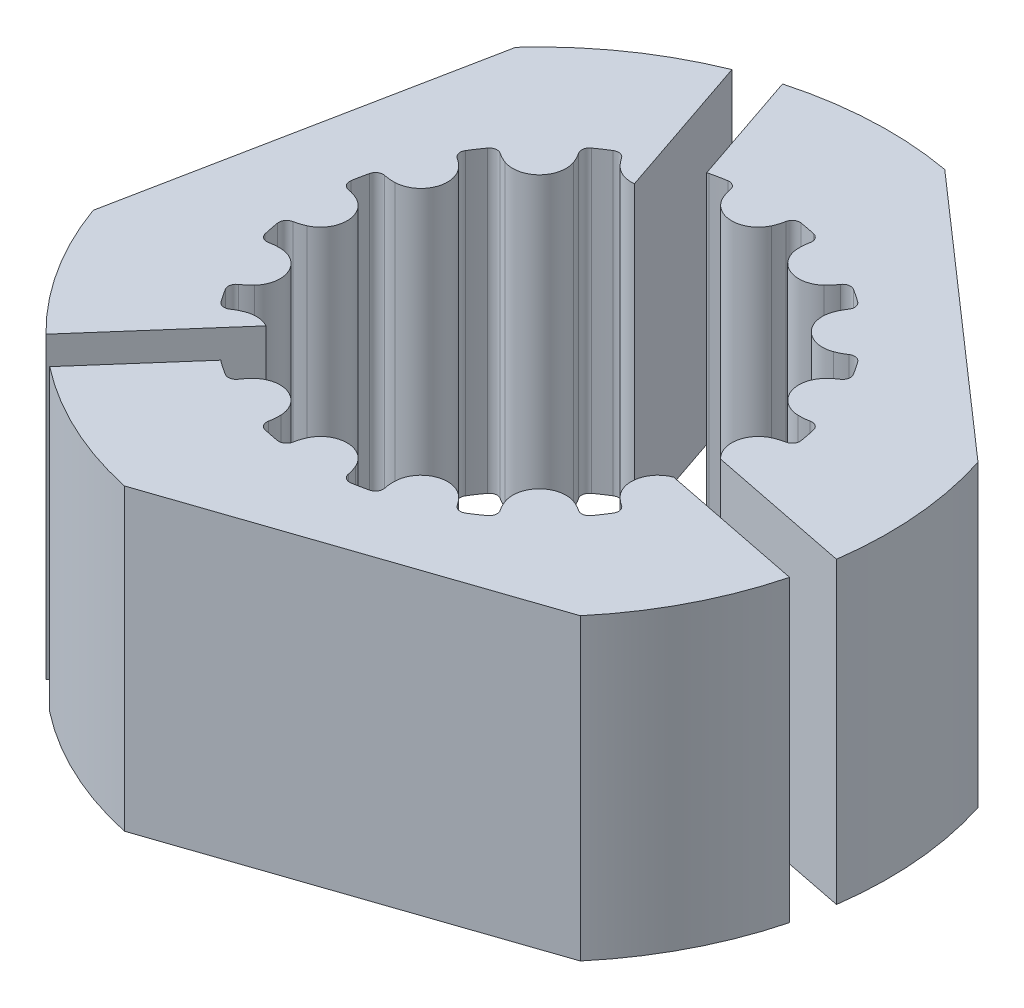
SolidWorks part; units mm, degrees
material "Alum Plate"
ref_plane "Front Plane" through (0, 0, 0) normal (0, 0, 1) x (1, 0, 0)
ref_plane "Top Plane" through (0, 0, 0) normal (0, 1, 0) x (1, 0, 0)
ref_plane "Right Plane" through (0, 0, 0) normal (1, 0, 0) x (0, 0, -1)
other "Bounding Box"
ref_plane "Default Plane" through (-8.9266, -12.7485, 0) normal (-0.1736, 0.9848, 0) x (0.9848, 0.1736, 0)
sketch "Sketch1" plane through (0, 0, 0) normal (0, 1, 0) x (1, 0, 0)
  line L0 (0, -7.8245) -> (0, 0) construction
  circle A0 centre (0, 0) radius 2.5
  arc B0 (-1.8508, -6.777) -> (-1.6633, -7.0715) centre (-1.6061, -6.8282) ccw
  arc B1 (-1.6633, -7.0715) -> (-1.1695, -7.1697) centre (0, 0) ccw
  arc B2 (-1.1695, -7.1697) -> (-0.8836, -6.9694) centre (-1.1292, -6.923) ccw
  arc B3 (-0.7739, -6.6229) -> (-0.8836, -6.9694) centre (0.61, -7.2516) ccw
  arc B4 (0.7739, -6.6229) -> (-0.7739, -6.6229) centre (0, -6.9745) ccw
  arc B5 (0.8836, -6.9694) -> (0.7739, -6.6229) centre (-0.61, -7.2516) ccw
  arc B6 (0.8836, -6.9694) -> (1.1695, -7.1697) centre (1.1292, -6.923) ccw
  arc B7 (1.1695, -7.1697) -> (1.6633, -7.0715) centre (0, 0) ccw
  arc B8 (1.6633, -7.0715) -> (1.8508, -6.777) centre (1.6061, -6.8282) ccw
  arc B9 (1.8195, -6.4149) -> (1.8508, -6.777) centre (3.3386, -6.4662) ccw
  arc B10 (3.2495, -5.8226) -> (1.8195, -6.4149) centre (2.669, -6.4436) ccw
  arc B11 (3.4834, -6.1008) -> (3.2495, -5.8226) centre (2.2115, -6.9331) ccw
  arc B12 (3.4834, -6.1008) -> (3.8242, -6.1764) centre (3.6926, -5.9639) ccw
  arc B13 (3.8242, -6.1764) -> (4.2428, -5.8967) centre (0, 0) ccw
  arc B14 (4.2428, -5.8967) -> (4.3033, -5.5529) centre (4.0968, -5.6938) ccw
  arc B15 (4.1359, -5.2303) -> (4.3033, -5.5529) centre (5.559, -4.6963) ccw
  arc B16 (5.2303, -4.1359) -> (4.1359, -5.2303) centre (4.9317, -4.9317) ccw
  arc B17 (5.5529, -4.3033) -> (5.2303, -4.1359) centre (4.6963, -5.559) ccw
  arc B18 (5.5529, -4.3033) -> (5.8967, -4.2428) centre (5.6938, -4.0968) ccw
  arc B19 (5.8967, -4.2428) -> (6.1764, -3.8242) centre (0, 0) ccw
  arc B20 (6.1764, -3.8242) -> (6.1008, -3.4834) centre (5.9639, -3.6926) ccw
  arc B21 (5.8226, -3.2495) -> (6.1008, -3.4834) centre (6.9331, -2.2115) ccw
  arc B22 (6.4149, -1.8195) -> (5.8226, -3.2495) centre (6.4436, -2.669) ccw
  arc B23 (6.777, -1.8508) -> (6.4149, -1.8195) centre (6.4662, -3.3386) ccw
  arc B24 (6.777, -1.8508) -> (7.0715, -1.6633) centre (6.8282, -1.6061) ccw
  arc B25 (7.0715, -1.6633) -> (7.1697, -1.1695) centre (0, 0) ccw
  arc B26 (7.1697, -1.1695) -> (6.9694, -0.8836) centre (6.923, -1.1292) ccw
  arc B27 (6.6229, -0.7739) -> (6.9694, -0.8836) centre (7.2516, 0.61) ccw
  arc B28 (6.6229, 0.7739) -> (6.6229, -0.7739) centre (6.9745, 0) ccw
  arc B29 (6.9694, 0.8836) -> (6.6229, 0.7739) centre (7.2516, -0.61) ccw
  arc B30 (6.9694, 0.8836) -> (7.1697, 1.1695) centre (6.923, 1.1292) ccw
  arc B31 (7.1697, 1.1695) -> (7.0715, 1.6633) centre (0, 0) ccw
  arc B32 (7.0715, 1.6633) -> (6.777, 1.8508) centre (6.8282, 1.6061) ccw
  arc B33 (6.4149, 1.8195) -> (6.777, 1.8508) centre (6.4662, 3.3386) ccw
  arc B34 (5.8226, 3.2495) -> (6.4149, 1.8195) centre (6.4436, 2.669) ccw
  arc B35 (6.1008, 3.4834) -> (5.8226, 3.2495) centre (6.9331, 2.2115) ccw
  arc B36 (6.1008, 3.4834) -> (6.1764, 3.8242) centre (5.9639, 3.6926) ccw
  arc B37 (6.1764, 3.8242) -> (5.8967, 4.2428) centre (0, 0) ccw
  arc B38 (5.8967, 4.2428) -> (5.5529, 4.3033) centre (5.6938, 4.0968) ccw
  arc B39 (5.2303, 4.1359) -> (5.5529, 4.3033) centre (4.6963, 5.559) ccw
  arc B40 (4.1359, 5.2303) -> (5.2303, 4.1359) centre (4.9317, 4.9317) ccw
  arc B41 (4.3033, 5.5529) -> (4.1359, 5.2303) centre (5.559, 4.6963) ccw
  arc B42 (4.3033, 5.5529) -> (4.2428, 5.8967) centre (4.0968, 5.6938) ccw
  arc B43 (4.2428, 5.8967) -> (3.8242, 6.1764) centre (0, 0) ccw
  arc B44 (3.8242, 6.1764) -> (3.4834, 6.1008) centre (3.6926, 5.9639) ccw
  arc B45 (3.2495, 5.8226) -> (3.4834, 6.1008) centre (2.2115, 6.9331) ccw
  arc B46 (1.8195, 6.4149) -> (3.2495, 5.8226) centre (2.669, 6.4436) ccw
  arc B47 (1.8508, 6.777) -> (1.8195, 6.4149) centre (3.3386, 6.4662) ccw
  arc B48 (1.8508, 6.777) -> (1.6633, 7.0715) centre (1.6061, 6.8282) ccw
  arc B49 (1.6633, 7.0715) -> (1.1695, 7.1697) centre (0, 0) ccw
  arc B50 (1.1695, 7.1697) -> (0.8836, 6.9694) centre (1.1292, 6.923) ccw
  arc B51 (0.7739, 6.6229) -> (0.8836, 6.9694) centre (-0.61, 7.2516) ccw
  arc B52 (-0.7739, 6.6229) -> (0.7739, 6.6229) centre (0, 6.9745) ccw
  arc B53 (-0.8836, 6.9694) -> (-0.7739, 6.6229) centre (0.61, 7.2516) ccw
  arc B54 (-0.8836, 6.9694) -> (-1.1695, 7.1697) centre (-1.1292, 6.923) ccw
  arc B55 (-1.1695, 7.1697) -> (-1.6633, 7.0715) centre (0, 0) ccw
  arc B56 (-1.6633, 7.0715) -> (-1.8508, 6.777) centre (-1.6061, 6.8282) ccw
  arc B57 (-1.8195, 6.4149) -> (-1.8508, 6.777) centre (-3.3386, 6.4662) ccw
  arc B58 (-3.2495, 5.8226) -> (-1.8195, 6.4149) centre (-2.669, 6.4436) ccw
  arc B59 (-3.4834, 6.1008) -> (-3.2495, 5.8226) centre (-2.2115, 6.9331) ccw
  arc B60 (-3.4834, 6.1008) -> (-3.8242, 6.1764) centre (-3.6926, 5.9639) ccw
  arc B61 (-3.8242, 6.1764) -> (-4.2428, 5.8967) centre (0, 0) ccw
  arc B62 (-4.2428, 5.8967) -> (-4.3033, 5.5529) centre (-4.0968, 5.6938) ccw
  arc B63 (-4.1359, 5.2303) -> (-4.3033, 5.5529) centre (-5.559, 4.6963) ccw
  arc B64 (-5.2303, 4.1359) -> (-4.1359, 5.2303) centre (-4.9317, 4.9317) ccw
  arc B65 (-5.5529, 4.3033) -> (-5.2303, 4.1359) centre (-4.6963, 5.559) ccw
  arc B66 (-5.5529, 4.3033) -> (-5.8967, 4.2428) centre (-5.6938, 4.0968) ccw
  arc B67 (-5.8967, 4.2428) -> (-6.1764, 3.8242) centre (0, 0) ccw
  arc B68 (-6.1764, 3.8242) -> (-6.1008, 3.4834) centre (-5.9639, 3.6926) ccw
  arc B69 (-5.8226, 3.2495) -> (-6.1008, 3.4834) centre (-6.9331, 2.2115) ccw
  arc B70 (-6.4149, 1.8195) -> (-5.8226, 3.2495) centre (-6.4436, 2.669) ccw
  arc B71 (-6.777, 1.8508) -> (-6.4149, 1.8195) centre (-6.4662, 3.3386) ccw
  arc B72 (-6.777, 1.8508) -> (-7.0715, 1.6633) centre (-6.8282, 1.6061) ccw
  arc B73 (-7.0715, 1.6633) -> (-7.1697, 1.1695) centre (0, 0) ccw
  arc B74 (-7.1697, 1.1695) -> (-6.9694, 0.8836) centre (-6.923, 1.1292) ccw
  arc B75 (-6.6229, 0.7739) -> (-6.9694, 0.8836) centre (-7.2516, -0.61) ccw
  arc B76 (-6.6229, -0.7739) -> (-6.6229, 0.7739) centre (-6.9745, 0) ccw
  arc B77 (-6.9694, -0.8836) -> (-6.6229, -0.7739) centre (-7.2516, 0.61) ccw
  arc B78 (-6.9694, -0.8836) -> (-7.1697, -1.1695) centre (-6.923, -1.1292) ccw
  arc B79 (-7.1697, -1.1695) -> (-7.0715, -1.6633) centre (0, 0) ccw
  arc B80 (-7.0715, -1.6633) -> (-6.777, -1.8508) centre (-6.8282, -1.6061) ccw
  arc B81 (-6.4149, -1.8195) -> (-6.777, -1.8508) centre (-6.4662, -3.3386) ccw
  arc B82 (-5.8226, -3.2495) -> (-6.4149, -1.8195) centre (-6.4436, -2.669) ccw
  arc B83 (-6.1008, -3.4834) -> (-5.8226, -3.2495) centre (-6.9331, -2.2115) ccw
  arc B84 (-6.1008, -3.4834) -> (-6.1764, -3.8242) centre (-5.9639, -3.6926) ccw
  arc B85 (-6.1764, -3.8242) -> (-5.8967, -4.2428) centre (0, 0) ccw
  arc B86 (-5.8967, -4.2428) -> (-5.5529, -4.3033) centre (-5.6938, -4.0968) ccw
  arc B87 (-5.2303, -4.1359) -> (-5.5529, -4.3033) centre (-4.6963, -5.559) ccw
  arc B88 (-4.1359, -5.2303) -> (-5.2303, -4.1359) centre (-4.9317, -4.9317) ccw
  arc B89 (-4.3033, -5.5529) -> (-4.1359, -5.2303) centre (-5.559, -4.6963) ccw
  arc B90 (-4.3033, -5.5529) -> (-4.2428, -5.8967) centre (-4.0968, -5.6938) ccw
  arc B91 (-4.2428, -5.8967) -> (-3.8242, -6.1764) centre (0, 0) ccw
  arc B92 (-3.8242, -6.1764) -> (-3.4834, -6.1008) centre (-3.6926, -5.9639) ccw
  arc B93 (-3.2495, -5.8226) -> (-3.4834, -6.1008) centre (-2.2115, -6.9331) ccw
  arc B94 (-1.8195, -6.4149) -> (-3.2495, -5.8226) centre (-2.669, -6.4436) ccw
  arc B95 (-1.8508, -6.777) -> (-1.8195, -6.4149) centre (-3.3386, -6.4662) ccw
  dimension "D1" = 5
sketch_block_instance "Block-GT2 16 Tooth Profile-1"
sketch_block "Block-GT2 16 Tooth Profile"
extrude "Boss-Extrude1" add sketch "Sketch1" along normal mid plane 9.525
sketch "Sketch2" plane through (0, -4.7625, 0) normal (0, -1, 0) x (1, 0, 0)
  circle A0 centre (0, 0) radius 7.9375
  circle A1 centre (0, 0) radius 2.5 construction
  circle A2 centre (0, 0) radius 2.5
  dimension "D1" = 15.875
extrude "Boss-Extrude2" add sketch "Sketch2" along normal blind 0.762 separate body
sketch "Sketch4" plane through (0, -4.7625, 0) normal (0, -1, 0) x (1, 0, 0)
  line L0 (-4.3596, 0.8672) -> (0, 0) construction
  line L1 (0, 0) -> (4.3596, -0.8672) construction
  line L2 (-7.1249, 1.4172) -> (-4.3596, 0.8672) construction
  circle A0 centre (-4.3596, 0.8672) radius 1
  circle A1 centre (4.3596, -0.8672) radius 1
  arc A2 (-7.0715, 1.6633) -> (-7.1697, 1.1695) centre (0, 0) ccw construction
  dimension "D1" = 2
  dimension "D2" = 4.445
extrude "Cut-Extrude2" cut sketch "Sketch4" against normal through all
sketch "Sketch5" plane through (0, -4.7625, 0) normal (0, 1, 0) x (1, 0, 0)
  circle A0 centre (-4.3596, -0.8672) radius 1.25
  circle A1 centre (4.3596, 0.8672) radius 1.25
  dimension "D1" = 2.5
extrude "Cut-Extrude3" cut sketch "Sketch5" against normal through all
delete or keep bodies "Body-Delete/Keep 1" [suppressed] type delete bodies bodies 111
delete or keep bodies "Body-Delete/Keep 2" [suppressed] type delete bodies bodies 108
sketch "Sketch6" plane through (0, 4.7625, 0) normal (0, 1, 0) x (1, 0, 0)
  line L2 (0, 0) -> (-3.572, 10.5228) construction
  line L3 (-7.327, -8.3548) -> (0, 0) construction
  line L4 (0, 0) -> (10.899, -2.1679) construction
  line L5 (-3.572, 10.5228) -> (10.899, -2.1679) construction
  line L6 (10.899, -2.1679) -> (-7.327, -8.3548) construction
  line L7 (-7.327, -8.3548) -> (-3.572, 10.5228) construction
  line L8 (-3.572, 10.5228) -> (-10.899, 2.1679) construction
  line L9 (-10.899, 2.1679) -> (-7.327, -8.3548) construction
  line L10 (-7.327, -8.3548) -> (3.572, -10.5228) construction
  line L11 (3.572, -10.5228) -> (10.899, -2.1679) construction
  line L12 (10.899, -2.1679) -> (7.327, 8.3548) construction
  line L13 (7.327, 8.3548) -> (-3.572, 10.5228) construction
  line L14 (0.6013, 0.2041) -> (-2.9707, 10.7269)
  line L15 (-6.8496, -8.7735) -> (0.4774, -0.4187)
  line L16 (-0.1239, -0.6228) -> (10.7751, -2.7907)
  line L17 (-0.6013, -0.2041) -> (-4.1733, 10.3186)
  line L18 (-7.8044, -7.9361) -> (-0.4774, 0.4187)
  line L19 (0.1239, 0.6228) -> (11.0229, -1.5451)
  line L20 (-8.2253, 7.4721) -> (-10.4586, -3.7556)
  line L21 (-2.3583, -10.8594) -> (8.4818, -7.1797)
  line L22 (1.9769, 10.9352) -> (10.5837, 3.3873)
  line L23 (7.327, 8.3548) -> (6.2803, 7.1613) construction
  line L24 (3.0617, -9.0195) -> (3.572, -10.5228) construction
  line L25 (-10.899, 2.1679) -> (-9.342, 1.8582) construction
  circle A1 centre (0, 0) radius 11.1125
  arc A96 (-1.8508, -6.777) -> (-1.8195, -6.4149) centre (-3.3386, -6.4662) ccw
  arc A97 (-1.8508, -6.777) -> (-1.6633, -7.0715) centre (-1.6061, -6.8282) ccw
  arc A98 (-1.6633, -7.0715) -> (-1.1695, -7.1697) centre (0, 0) ccw
  arc A99 (-1.1695, -7.1697) -> (-0.8836, -6.9694) centre (-1.1292, -6.923) ccw
  arc A100 (-0.7739, -6.6229) -> (-0.8836, -6.9694) centre (0.61, -7.2516) ccw
  arc A101 (0.7739, -6.6229) -> (-0.7739, -6.6229) centre (0, -6.9745) ccw
  arc A102 (0.8836, -6.9694) -> (0.7739, -6.6229) centre (-0.61, -7.2516) ccw
  arc A103 (0.8836, -6.9694) -> (1.1695, -7.1697) centre (1.1292, -6.923) ccw
  arc A104 (1.1695, -7.1697) -> (1.6633, -7.0715) centre (0, 0) ccw
  arc A105 (1.6633, -7.0715) -> (1.8508, -6.777) centre (1.6061, -6.8282) ccw
  arc A106 (1.8195, -6.4149) -> (1.8508, -6.777) centre (3.3386, -6.4662) ccw
  arc A107 (3.2495, -5.8226) -> (1.8195, -6.4149) centre (2.669, -6.4436) ccw
  arc A108 (3.4834, -6.1008) -> (3.2495, -5.8226) centre (2.2115, -6.9331) ccw
  arc A109 (3.4834, -6.1008) -> (3.8242, -6.1764) centre (3.6926, -5.9639) ccw
  arc A110 (3.8242, -6.1764) -> (4.2428, -5.8967) centre (0, 0) ccw
  arc A111 (4.2428, -5.8967) -> (4.3033, -5.5529) centre (4.0968, -5.6938) ccw
  arc A112 (4.1359, -5.2303) -> (4.3033, -5.5529) centre (5.559, -4.6963) ccw
  arc A113 (5.2303, -4.1359) -> (4.1359, -5.2303) centre (4.9317, -4.9317) ccw
  arc A114 (5.5529, -4.3033) -> (5.2303, -4.1359) centre (4.6963, -5.559) ccw
  arc A115 (5.5529, -4.3033) -> (5.8967, -4.2428) centre (5.6938, -4.0968) ccw
  arc A116 (5.8967, -4.2428) -> (6.1764, -3.8242) centre (0, 0) ccw
  arc A117 (6.1764, -3.8242) -> (6.1008, -3.4834) centre (5.9639, -3.6926) ccw
  arc A118 (5.8226, -3.2495) -> (6.1008, -3.4834) centre (6.9331, -2.2115) ccw
  arc A119 (6.4149, -1.8195) -> (5.8226, -3.2495) centre (6.4436, -2.669) ccw
  arc A120 (6.777, -1.8508) -> (6.4149, -1.8195) centre (6.4662, -3.3386) ccw
  arc A121 (6.777, -1.8508) -> (7.0715, -1.6633) centre (6.8282, -1.6061) ccw
  arc A122 (7.0715, -1.6633) -> (7.1697, -1.1695) centre (0, 0) ccw
  arc A123 (7.1697, -1.1695) -> (6.9694, -0.8836) centre (6.923, -1.1292) ccw
  arc A124 (6.6229, -0.7739) -> (6.9694, -0.8836) centre (7.2516, 0.61) ccw
  arc A125 (6.6229, 0.7739) -> (6.6229, -0.7739) centre (6.9745, 0) ccw
  arc A126 (6.9694, 0.8836) -> (6.6229, 0.7739) centre (7.2516, -0.61) ccw
  arc A127 (6.9694, 0.8836) -> (7.1697, 1.1695) centre (6.923, 1.1292) ccw
  arc A128 (7.1697, 1.1695) -> (7.0715, 1.6633) centre (0, 0) ccw
  arc A129 (7.0715, 1.6633) -> (6.777, 1.8508) centre (6.8282, 1.6061) ccw
  arc A130 (6.4149, 1.8195) -> (6.777, 1.8508) centre (6.4662, 3.3386) ccw
  arc A131 (5.8226, 3.2495) -> (6.4149, 1.8195) centre (6.4436, 2.669) ccw
  arc A132 (6.1008, 3.4834) -> (5.8226, 3.2495) centre (6.9331, 2.2115) ccw
  arc A133 (6.1008, 3.4834) -> (6.1764, 3.8242) centre (5.9639, 3.6926) ccw
  arc A134 (6.1764, 3.8242) -> (5.8967, 4.2428) centre (0, 0) ccw
  arc A135 (5.8967, 4.2428) -> (5.5529, 4.3033) centre (5.6938, 4.0968) ccw
  arc A136 (5.2303, 4.1359) -> (5.5529, 4.3033) centre (4.6963, 5.559) ccw
  arc A137 (4.1359, 5.2303) -> (5.2303, 4.1359) centre (4.9317, 4.9317) ccw
  arc A138 (4.3033, 5.5529) -> (4.1359, 5.2303) centre (5.559, 4.6963) ccw
  arc A139 (4.3033, 5.5529) -> (4.2428, 5.8967) centre (4.0968, 5.6938) ccw
  arc A140 (4.2428, 5.8967) -> (3.8242, 6.1764) centre (0, 0) ccw
  arc A141 (3.8242, 6.1764) -> (3.4834, 6.1008) centre (3.6926, 5.9639) ccw
  arc A142 (3.2495, 5.8226) -> (3.4834, 6.1008) centre (2.2115, 6.9331) ccw
  arc A143 (1.8195, 6.4149) -> (3.2495, 5.8226) centre (2.669, 6.4436) ccw
  arc A144 (1.8508, 6.777) -> (1.8195, 6.4149) centre (3.3386, 6.4662) ccw
  arc A145 (1.8508, 6.777) -> (1.6633, 7.0715) centre (1.6061, 6.8282) ccw
  arc A146 (1.6633, 7.0715) -> (1.1695, 7.1697) centre (0, 0) ccw
  arc A147 (1.1695, 7.1697) -> (0.8836, 6.9694) centre (1.1292, 6.923) ccw
  arc A148 (0.7739, 6.6229) -> (0.8836, 6.9694) centre (-0.61, 7.2516) ccw
  arc A149 (-0.7739, 6.6229) -> (0.7739, 6.6229) centre (0, 6.9745) ccw
  arc A150 (-0.8836, 6.9694) -> (-0.7739, 6.6229) centre (0.61, 7.2516) ccw
  arc A151 (-0.8836, 6.9694) -> (-1.1695, 7.1697) centre (-1.1292, 6.923) ccw
  arc A152 (-1.1695, 7.1697) -> (-1.6633, 7.0715) centre (0, 0) ccw
  arc A153 (-1.6633, 7.0715) -> (-1.8508, 6.777) centre (-1.6061, 6.8282) ccw
  arc A154 (-1.8195, 6.4149) -> (-1.8508, 6.777) centre (-3.3386, 6.4662) ccw
  arc A155 (-3.2495, 5.8226) -> (-1.8195, 6.4149) centre (-2.669, 6.4436) ccw
  arc A156 (-3.4834, 6.1008) -> (-3.2495, 5.8226) centre (-2.2115, 6.9331) ccw
  arc A157 (-3.4834, 6.1008) -> (-3.8242, 6.1764) centre (-3.6926, 5.9639) ccw
  arc A158 (-3.8242, 6.1764) -> (-4.2428, 5.8967) centre (0, 0) ccw
  arc A159 (-4.2428, 5.8967) -> (-4.3033, 5.5529) centre (-4.0968, 5.6938) ccw
  arc A160 (-4.1359, 5.2303) -> (-4.3033, 5.5529) centre (-5.559, 4.6963) ccw
  arc A161 (-5.2303, 4.1359) -> (-4.1359, 5.2303) centre (-4.9317, 4.9317) ccw
  arc A162 (-5.5529, 4.3033) -> (-5.2303, 4.1359) centre (-4.6963, 5.559) ccw
  arc A163 (-5.5529, 4.3033) -> (-5.8967, 4.2428) centre (-5.6938, 4.0968) ccw
  arc A164 (-5.8967, 4.2428) -> (-6.1764, 3.8242) centre (0, 0) ccw
  arc A165 (-6.1764, 3.8242) -> (-6.1008, 3.4834) centre (-5.9639, 3.6926) ccw
  arc A166 (-5.8226, 3.2495) -> (-6.1008, 3.4834) centre (-6.9331, 2.2115) ccw
  arc A167 (-6.4149, 1.8195) -> (-5.8226, 3.2495) centre (-6.4436, 2.669) ccw
  arc A168 (-6.777, 1.8508) -> (-6.4149, 1.8195) centre (-6.4662, 3.3386) ccw
  arc A169 (-6.777, 1.8508) -> (-7.0715, 1.6633) centre (-6.8282, 1.6061) ccw
  arc A170 (-7.0715, 1.6633) -> (-7.1697, 1.1695) centre (0, 0) ccw
  arc A171 (-7.1697, 1.1695) -> (-6.9694, 0.8836) centre (-6.923, 1.1292) ccw
  arc A172 (-6.6229, 0.7739) -> (-6.9694, 0.8836) centre (-7.2516, -0.61) ccw
  arc A173 (-6.6229, -0.7739) -> (-6.6229, 0.7739) centre (-6.9745, 0) ccw
  arc A174 (-6.9694, -0.8836) -> (-6.6229, -0.7739) centre (-7.2516, 0.61) ccw
  arc A175 (-6.9694, -0.8836) -> (-7.1697, -1.1695) centre (-6.923, -1.1292) ccw
  arc A176 (-7.1697, -1.1695) -> (-7.0715, -1.6633) centre (0, 0) ccw
  arc A177 (-7.0715, -1.6633) -> (-6.777, -1.8508) centre (-6.8282, -1.6061) ccw
  arc A178 (-6.4149, -1.8195) -> (-6.777, -1.8508) centre (-6.4662, -3.3386) ccw
  arc A179 (-5.8226, -3.2495) -> (-6.4149, -1.8195) centre (-6.4436, -2.669) ccw
  arc A180 (-6.1008, -3.4834) -> (-5.8226, -3.2495) centre (-6.9331, -2.2115) ccw
  arc A181 (-6.1008, -3.4834) -> (-6.1764, -3.8242) centre (-5.9639, -3.6926) ccw
  arc A182 (-6.1764, -3.8242) -> (-5.8967, -4.2428) centre (0, 0) ccw
  arc A183 (-5.8967, -4.2428) -> (-5.5529, -4.3033) centre (-5.6938, -4.0968) ccw
  arc A184 (-5.2303, -4.1359) -> (-5.5529, -4.3033) centre (-4.6963, -5.559) ccw
  arc A185 (-4.1359, -5.2303) -> (-5.2303, -4.1359) centre (-4.9317, -4.9317) ccw
  arc A186 (-4.3033, -5.5529) -> (-4.1359, -5.2303) centre (-5.559, -4.6963) ccw
  arc A187 (-4.3033, -5.5529) -> (-4.2428, -5.8967) centre (-4.0968, -5.6938) ccw
  arc A188 (-4.2428, -5.8967) -> (-3.8242, -6.1764) centre (0, 0) ccw
  arc A189 (-3.8242, -6.1764) -> (-3.4834, -6.1008) centre (-3.6926, -5.9639) ccw
  arc A190 (-3.2495, -5.8226) -> (-3.4834, -6.1008) centre (-2.2115, -6.9331) ccw
  arc A191 (-1.8195, -6.4149) -> (-3.2495, -5.8226) centre (-2.669, -6.4436) ccw
  arc A192 (-1.8508, -6.777) -> (-1.8195, -6.4149) centre (-3.3386, -6.4662) ccw
  arc A193 (-1.8508, -6.777) -> (-1.6633, -7.0715) centre (-1.6061, -6.8282) ccw
  arc A194 (-1.6633, -7.0715) -> (-1.1695, -7.1697) centre (0, 0) ccw
  arc A195 (-1.1695, -7.1697) -> (-0.8836, -6.9694) centre (-1.1292, -6.923) ccw
  arc A196 (-0.7739, -6.6229) -> (-0.8836, -6.9694) centre (0.61, -7.2516) ccw
  arc A197 (0.7739, -6.6229) -> (-0.7739, -6.6229) centre (0, -6.9745) ccw
  arc A198 (0.8836, -6.9694) -> (0.7739, -6.6229) centre (-0.61, -7.2516) ccw
  arc A199 (0.8836, -6.9694) -> (1.1695, -7.1697) centre (1.1292, -6.923) ccw
  arc A200 (1.1695, -7.1697) -> (1.6633, -7.0715) centre (0, 0) ccw
  arc A201 (1.6633, -7.0715) -> (1.8508, -6.777) centre (1.6061, -6.8282) ccw
  arc A202 (1.8195, -6.4149) -> (1.8508, -6.777) centre (3.3386, -6.4662) ccw
  arc A203 (3.2495, -5.8226) -> (1.8195, -6.4149) centre (2.669, -6.4436) ccw
  arc A204 (3.4834, -6.1008) -> (3.2495, -5.8226) centre (2.2115, -6.9331) ccw
  arc A205 (3.4834, -6.1008) -> (3.8242, -6.1764) centre (3.6926, -5.9639) ccw
  arc A206 (3.8242, -6.1764) -> (4.2428, -5.8967) centre (0, 0) ccw
  arc A207 (4.2428, -5.8967) -> (4.3033, -5.5529) centre (4.0968, -5.6938) ccw
  arc A208 (4.1359, -5.2303) -> (4.3033, -5.5529) centre (5.559, -4.6963) ccw
  arc A209 (5.2303, -4.1359) -> (4.1359, -5.2303) centre (4.9317, -4.9317) ccw
  arc A210 (5.5529, -4.3033) -> (5.2303, -4.1359) centre (4.6963, -5.559) ccw
  arc A211 (5.5529, -4.3033) -> (5.8967, -4.2428) centre (5.6938, -4.0968) ccw
  arc A212 (5.8967, -4.2428) -> (6.1764, -3.8242) centre (0, 0) ccw
  arc A213 (6.1764, -3.8242) -> (6.1008, -3.4834) centre (5.9639, -3.6926) ccw
  arc A214 (5.8226, -3.2495) -> (6.1008, -3.4834) centre (6.9331, -2.2115) ccw
  arc A215 (6.4149, -1.8195) -> (5.8226, -3.2495) centre (6.4436, -2.669) ccw
  arc A216 (6.777, -1.8508) -> (6.4149, -1.8195) centre (6.4662, -3.3386) ccw
  arc A217 (6.777, -1.8508) -> (7.0715, -1.6633) centre (6.8282, -1.6061) ccw
  arc A218 (7.0715, -1.6633) -> (7.1697, -1.1695) centre (0, 0) ccw
  arc A219 (7.1697, -1.1695) -> (6.9694, -0.8836) centre (6.923, -1.1292) ccw
  arc A220 (6.6229, -0.7739) -> (6.9694, -0.8836) centre (7.2516, 0.61) ccw
  arc A221 (6.6229, 0.7739) -> (6.6229, -0.7739) centre (6.9745, 0) ccw
  arc A222 (6.9694, 0.8836) -> (6.6229, 0.7739) centre (7.2516, -0.61) ccw
  arc A223 (6.9694, 0.8836) -> (7.1697, 1.1695) centre (6.923, 1.1292) ccw
  arc A224 (7.1697, 1.1695) -> (7.0715, 1.6633) centre (0, 0) ccw
  arc A225 (7.0715, 1.6633) -> (6.777, 1.8508) centre (6.8282, 1.6061) ccw
  arc A226 (6.4149, 1.8195) -> (6.777, 1.8508) centre (6.4662, 3.3386) ccw
  arc A227 (5.8226, 3.2495) -> (6.4149, 1.8195) centre (6.4436, 2.669) ccw
  arc A228 (6.1008, 3.4834) -> (5.8226, 3.2495) centre (6.9331, 2.2115) ccw
  arc A229 (6.1008, 3.4834) -> (6.1764, 3.8242) centre (5.9639, 3.6926) ccw
  arc A230 (6.1764, 3.8242) -> (5.8967, 4.2428) centre (0, 0) ccw
  arc A231 (5.8967, 4.2428) -> (5.5529, 4.3033) centre (5.6938, 4.0968) ccw
  arc A232 (5.2303, 4.1359) -> (5.5529, 4.3033) centre (4.6963, 5.559) ccw
  arc A233 (4.1359, 5.2303) -> (5.2303, 4.1359) centre (4.9317, 4.9317) ccw
  arc A234 (4.3033, 5.5529) -> (4.1359, 5.2303) centre (5.559, 4.6963) ccw
  arc A235 (4.3033, 5.5529) -> (4.2428, 5.8967) centre (4.0968, 5.6938) ccw
  arc A236 (4.2428, 5.8967) -> (3.8242, 6.1764) centre (0, 0) ccw
  arc A237 (3.8242, 6.1764) -> (3.4834, 6.1008) centre (3.6926, 5.9639) ccw
  arc A238 (3.2495, 5.8226) -> (3.4834, 6.1008) centre (2.2115, 6.9331) ccw
  arc A239 (1.8195, 6.4149) -> (3.2495, 5.8226) centre (2.669, 6.4436) ccw
  arc A240 (1.8508, 6.777) -> (1.8195, 6.4149) centre (3.3386, 6.4662) ccw
  arc A241 (1.8508, 6.777) -> (1.6633, 7.0715) centre (1.6061, 6.8282) ccw
  arc A242 (1.6633, 7.0715) -> (1.1695, 7.1697) centre (0, 0) ccw
  arc A243 (1.1695, 7.1697) -> (0.8836, 6.9694) centre (1.1292, 6.923) ccw
  arc A244 (0.7739, 6.6229) -> (0.8836, 6.9694) centre (-0.61, 7.2516) ccw
  arc A245 (-0.7739, 6.6229) -> (0.7739, 6.6229) centre (0, 6.9745) ccw
  arc A246 (-0.8836, 6.9694) -> (-0.7739, 6.6229) centre (0.61, 7.2516) ccw
  arc A247 (-0.8836, 6.9694) -> (-1.1695, 7.1697) centre (-1.1292, 6.923) ccw
  arc A248 (-1.1695, 7.1697) -> (-1.6633, 7.0715) centre (0, 0) ccw
  arc A249 (-1.6633, 7.0715) -> (-1.8508, 6.777) centre (-1.6061, 6.8282) ccw
  arc A250 (-1.8195, 6.4149) -> (-1.8508, 6.777) centre (-3.3386, 6.4662) ccw
  arc A251 (-3.2495, 5.8226) -> (-1.8195, 6.4149) centre (-2.669, 6.4436) ccw
  arc A252 (-3.4834, 6.1008) -> (-3.2495, 5.8226) centre (-2.2115, 6.9331) ccw
  arc A253 (-3.4834, 6.1008) -> (-3.8242, 6.1764) centre (-3.6926, 5.9639) ccw
  arc A254 (-3.8242, 6.1764) -> (-4.2428, 5.8967) centre (0, 0) ccw
  arc A255 (-4.2428, 5.8967) -> (-4.3033, 5.5529) centre (-4.0968, 5.6938) ccw
  arc A256 (-4.1359, 5.2303) -> (-4.3033, 5.5529) centre (-5.559, 4.6963) ccw
  arc A257 (-5.2303, 4.1359) -> (-4.1359, 5.2303) centre (-4.9317, 4.9317) ccw
  arc A258 (-5.5529, 4.3033) -> (-5.2303, 4.1359) centre (-4.6963, 5.559) ccw
  arc A259 (-5.5529, 4.3033) -> (-5.8967, 4.2428) centre (-5.6938, 4.0968) ccw
  arc A260 (-5.8967, 4.2428) -> (-6.1764, 3.8242) centre (0, 0) ccw
  arc A261 (-6.1764, 3.8242) -> (-6.1008, 3.4834) centre (-5.9639, 3.6926) ccw
  arc A262 (-5.8226, 3.2495) -> (-6.1008, 3.4834) centre (-6.9331, 2.2115) ccw
  arc A263 (-6.4149, 1.8195) -> (-5.8226, 3.2495) centre (-6.4436, 2.669) ccw
  arc A264 (-6.777, 1.8508) -> (-6.4149, 1.8195) centre (-6.4662, 3.3386) ccw
  arc A265 (-6.777, 1.8508) -> (-7.0715, 1.6633) centre (-6.8282, 1.6061) ccw
  arc A266 (-7.0715, 1.6633) -> (-7.1697, 1.1695) centre (0, 0) ccw
  arc A267 (-7.1697, 1.1695) -> (-6.9694, 0.8836) centre (-6.923, 1.1292) ccw
  arc A268 (-6.6229, 0.7739) -> (-6.9694, 0.8836) centre (-7.2516, -0.61) ccw
  arc A269 (-6.6229, -0.7739) -> (-6.6229, 0.7739) centre (-6.9745, 0) ccw
  arc A270 (-6.9694, -0.8836) -> (-6.6229, -0.7739) centre (-7.2516, 0.61) ccw
  arc A271 (-6.9694, -0.8836) -> (-7.1697, -1.1695) centre (-6.923, -1.1292) ccw
  arc A272 (-7.1697, -1.1695) -> (-7.0715, -1.6633) centre (0, 0) ccw
  arc A273 (-7.0715, -1.6633) -> (-6.777, -1.8508) centre (-6.8282, -1.6061) ccw
  arc A274 (-6.4149, -1.8195) -> (-6.777, -1.8508) centre (-6.4662, -3.3386) ccw
  arc A275 (-5.8226, -3.2495) -> (-6.4149, -1.8195) centre (-6.4436, -2.669) ccw
  arc A276 (-6.1008, -3.4834) -> (-5.8226, -3.2495) centre (-6.9331, -2.2115) ccw
  arc A277 (-6.1008, -3.4834) -> (-6.1764, -3.8242) centre (-5.9639, -3.6926) ccw
  arc A278 (-6.1764, -3.8242) -> (-5.8967, -4.2428) centre (0, 0) ccw
  arc A279 (-5.8967, -4.2428) -> (-5.5529, -4.3033) centre (-5.6938, -4.0968) ccw
  arc A280 (-5.2303, -4.1359) -> (-5.5529, -4.3033) centre (-4.6963, -5.559) ccw
  arc A281 (-4.1359, -5.2303) -> (-5.2303, -4.1359) centre (-4.9317, -4.9317) ccw
  arc A282 (-4.3033, -5.5529) -> (-4.1359, -5.2303) centre (-5.559, -4.6963) ccw
  arc A283 (-4.3033, -5.5529) -> (-4.2428, -5.8967) centre (-4.0968, -5.6938) ccw
  arc A284 (-4.2428, -5.8967) -> (-3.8242, -6.1764) centre (0, 0) ccw
  arc A285 (-3.8242, -6.1764) -> (-3.4834, -6.1008) centre (-3.6926, -5.9639) ccw
  arc A286 (-3.2495, -5.8226) -> (-3.4834, -6.1008) centre (-2.2115, -6.9331) ccw
  arc A287 (-1.8195, -6.4149) -> (-3.2495, -5.8226) centre (-2.669, -6.4436) ccw
  point P99 (7.1249, -1.4172)
  dimension "D2" = 0.635
  dimension "D4" = 0.635
  dimension "D3" = 22.225
  dimension "D5" = 9.525
  dimension "D1" = 0
extrude "Boss-Extrude3" add sketch "Sketch6" against normal up to surface (9.525 mm away) separate body contours A192 A287 L17 A1 L20 L18 A221 A220 A219 A218 A217 A216 A215 A214 A213 A212 A211 A210 A209 A208 A207 A206 A205 A204 A203 A202 A201 A200 A199 A198 A197 A196 A195 A194 A193 | A284 A283 A282 A281 A280 A279 A278 A277 A276 A275 A274 A273 A272 A271 A270 A269 A268 A267 A266 A265 A264 A263 A262 A261 A260 A259 A258 A257 A256 A255 A254 L19 A1 L22 L14 | L16 A251 A250 A249 A248 A247 A246 A245 A244 A243 A242 A241 A240 A239 A238 A237 A236 A235 A234 A233 A232 A231 A230 A229 A228 A227 A226 A225 A224 A223 A222 A221 L15 A1 L21
delete or keep bodies "Body-Delete/Keep 3" type delete bodies bodies 108 111
